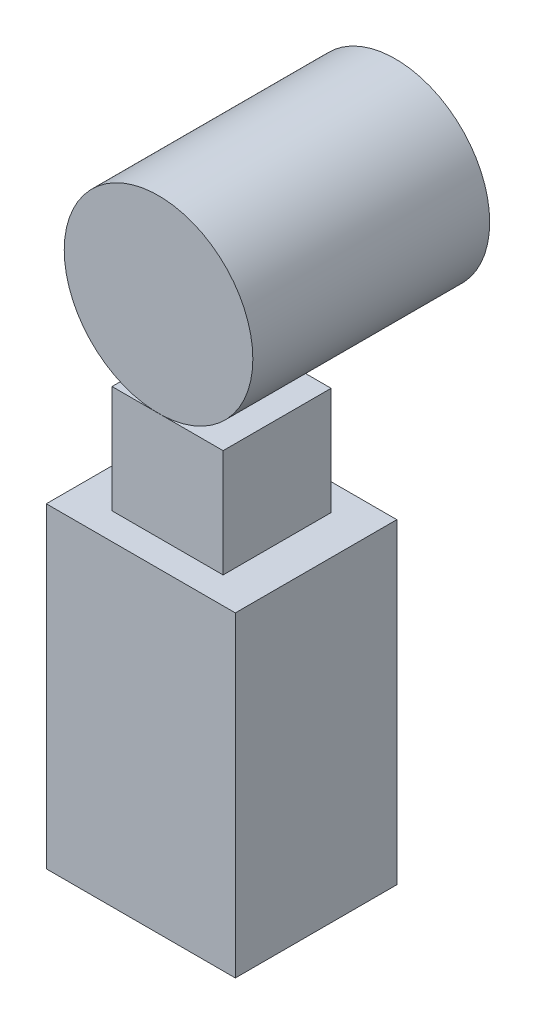
SolidWorks part; units mm, degrees
ref_plane "Front Plane" through (0, 0, 0) normal (0, 0, 1) x (1, 0, 0)
ref_plane "Top Plane" through (0, 0, 0) normal (0, 1, 0) x (1, 0, 0)
ref_plane "Right Plane" through (0, 0, 0) normal (1, 0, 0) x (0, 0, -1)
sketch "Sketch1" plane through (0, 0, 0) normal (0, 0, 1) x (1, 0, 0)
  line L1 (-51.5518, -71.8594) -> (18.6789, -71.8594)
  line L2 (-51.5518, -71.8594) -> (-51.5518, 45.6167)
  line L3 (-51.5518, 45.6167) -> (18.6789, 45.6167)
  line L4 (18.6789, -71.8594) -> (18.6789, 45.6167)
  line L5 (-51.5518, -71.8594) -> (18.6789, 45.6167) construction
  line L6 (-51.5518, 45.6167) -> (18.6789, -71.8594) construction
  point P0 (-16.4364, -13.1214)
extrude "Boss-Extrude1" add sketch "Sketch1" along normal blind 60
sketch "Sketch2" plane through (0, 45.6167, 0) normal (0, 1, 0) x (1, 0, 0)
  line L1 (4.2, -50.0657) -> (-37.0728, -50.0657)
  line L2 (4.2, -50.0657) -> (4.2, -9.9343)
  line L3 (4.2, -9.9343) -> (-37.0728, -9.9343)
  line L4 (-37.0728, -50.0657) -> (-37.0728, -9.9343)
  line L5 (4.2, -50.0657) -> (-37.0728, -9.9343) construction
  line L6 (4.2, -9.9343) -> (-37.0728, -50.0657) construction
  point P0 (-16.4364, -30)
extrude "Boss-Extrude2" add sketch "Sketch2" along normal blind 40
sketch "Sketch4" plane through (0, 0, 50.0657) normal (0, 0, 1) x (1, 0, 0)
  circle A0 centre (-19.7896, 120.6546) radius 35.0379
extrude "Boss-Extrude4" add sketch "Sketch4" against normal blind 88 separate body
